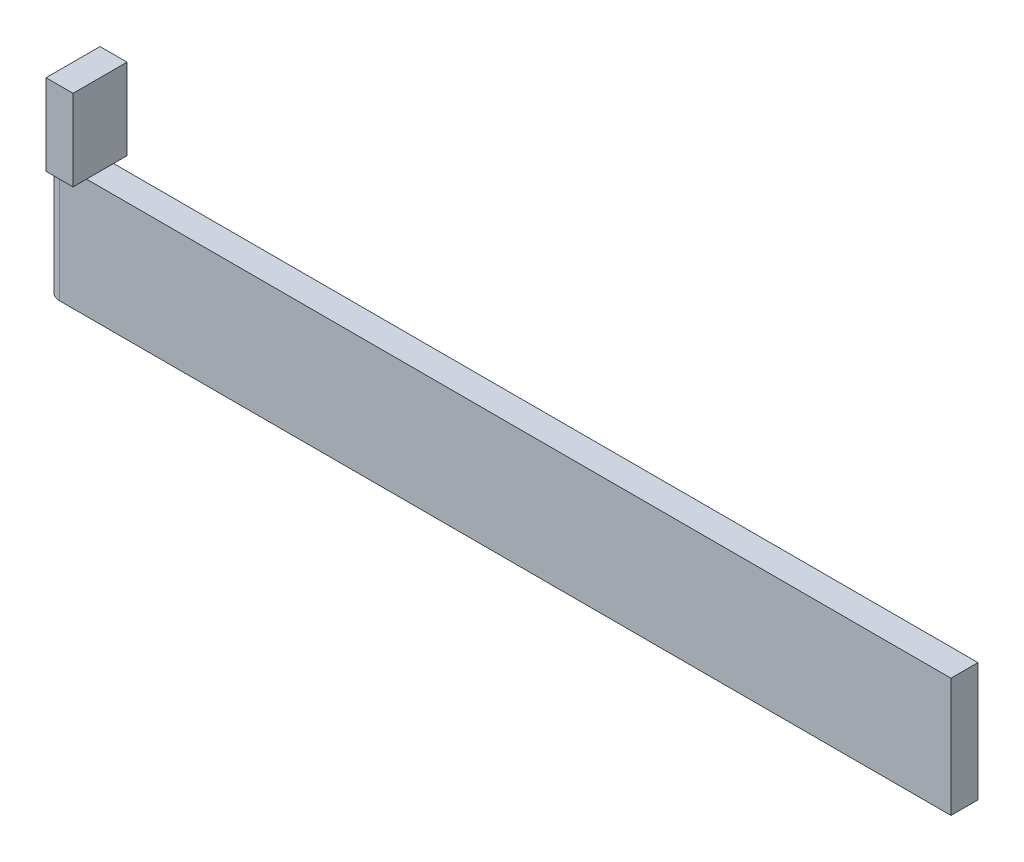
SolidWorks part; units mm, degrees
ref_plane "Front Plane" through (0, 0, 0) normal (0, 0, 1) x (1, 0, 0)
ref_plane "Top Plane" through (0, 0, 0) normal (0, 1, 0) x (1, 0, 0)
ref_plane "Right Plane" through (0, 0, 0) normal (1, 0, 0) x (0, 0, -1)
sketch "Sketch1" plane through (0, 0, 0) normal (0, 0, 1) x (1, 0, 0)
  line L1 (0, 0) -> (165, 0)
  line L2 (0, 0) -> (0, 22)
  line L3 (0, 22) -> (165, 22)
  line L4 (165, 0) -> (165, 22)
  dimension "D1" = 165
  dimension "D2" = 22
extrude "Boss-Extrude1" add sketch "Sketch1" along normal blind 5
sketch "Sketch2" plane through (0, 0, 0) normal (-1, 0, 0) x (0, 0, 1)
  line L1 (-2.5, 22) -> (7.5, 22)
  line L2 (-2.5, 22) -> (-2.5, 37)
  line L3 (-2.5, 37) -> (7.5, 37)
  line L4 (7.5, 22) -> (7.5, 37)
  line L7 (0, 22) -> (0, 0) construction
  line L8 (5, 22) -> (0, 22) construction
  dimension "D1" = 15
  dimension "D2" = 10
  dimension "D3" = 2.5
extrude "Boss-Extrude2" add sketch "Sketch2" against normal blind 5
sketch "Sketch3" plane through (0, 22, 0) normal (0, 1, 0) x (1, 0, 0)
  line L0 (0, -7.5) -> (0, 2.5) construction
  circle A0 centre (0, -2.5) radius 2.5
  point P0 (0, 0)
extrude "Boss-Extrude3" add sketch "Sketch3" against normal blind 22
